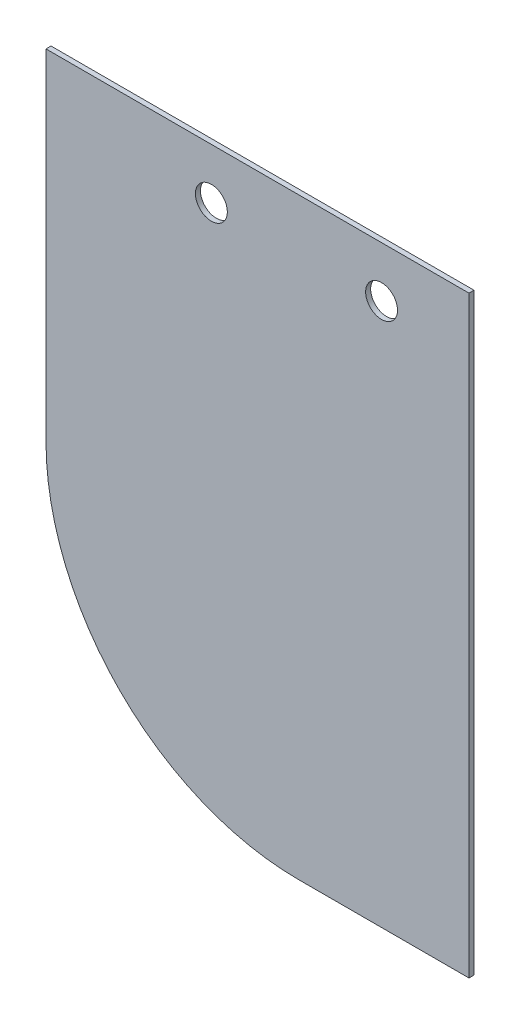
SolidWorks part; units mm, degrees
ref_plane "Front Plane" through (0, 0, 0) normal (0, 0, 1) x (1, 0, 0)
ref_plane "Top Plane" through (0, 0, 0) normal (0, 1, 0) x (1, 0, 0)
ref_plane "Right Plane" through (0, 0, 0) normal (1, 0, 0) x (0, 0, -1)
sketch "Sketch1" plane through (0, 0, 0) normal (0, 0, 1) x (1, 0, 0)
  line L0 (-545.175, 1066.8) -> (-545.175, 1168.4) construction
  line L1 (-418.175, 990.6) -> (-468.975, 990.6) construction
  line L2 (-545.175, 1066.8) -> (-545.175, 1168.4) construction
  line L3 (-418.175, 990.6) -> (-468.975, 990.6) construction
  line L4 (-418.175, 991.35) -> (-468.975, 991.35)
  line L5 (-544.425, 1066.8) -> (-544.425, 1168.4)
  line L6 (-418.175, 991.35) -> (-418.175, 1168.4)
  line L7 (-418.925, 1168.4) -> (-417.425, 1168.4) construction
  line L8 (-544.425, 1168.4) -> (-418.175, 1168.4)
  line L9 (-356.05, 1153.3) -> (-444.2625, 1153.3) construction
  line L10 (-490.3, 1181.1) -> (-490.3, 1148.3) construction
  line L11 (-439.5, 1181.1) -> (-439.5, 1148.3) construction
  arc A0 (-545.175, 1066.8) -> (-468.975, 990.6) centre (-468.975, 1066.8) ccw construction
  arc A1 (-545.175, 1066.8) -> (-468.975, 990.6) centre (-468.975, 1066.8) ccw construction
  arc A2 (-544.425, 1066.8) -> (-468.975, 991.35) centre (-468.975, 1066.8) ccw
  circle A3 centre (-444.2625, 1153.3) radius 4.7625
  circle A4 centre (-495.0625, 1153.3) radius 4.7625
  circle A5 centre (-356.05, 1153.3) radius 4.7625 construction
  dimension "D1" = 0.75
extrude "Extrude1" add sketch "Sketch1" along normal blind 1.5
